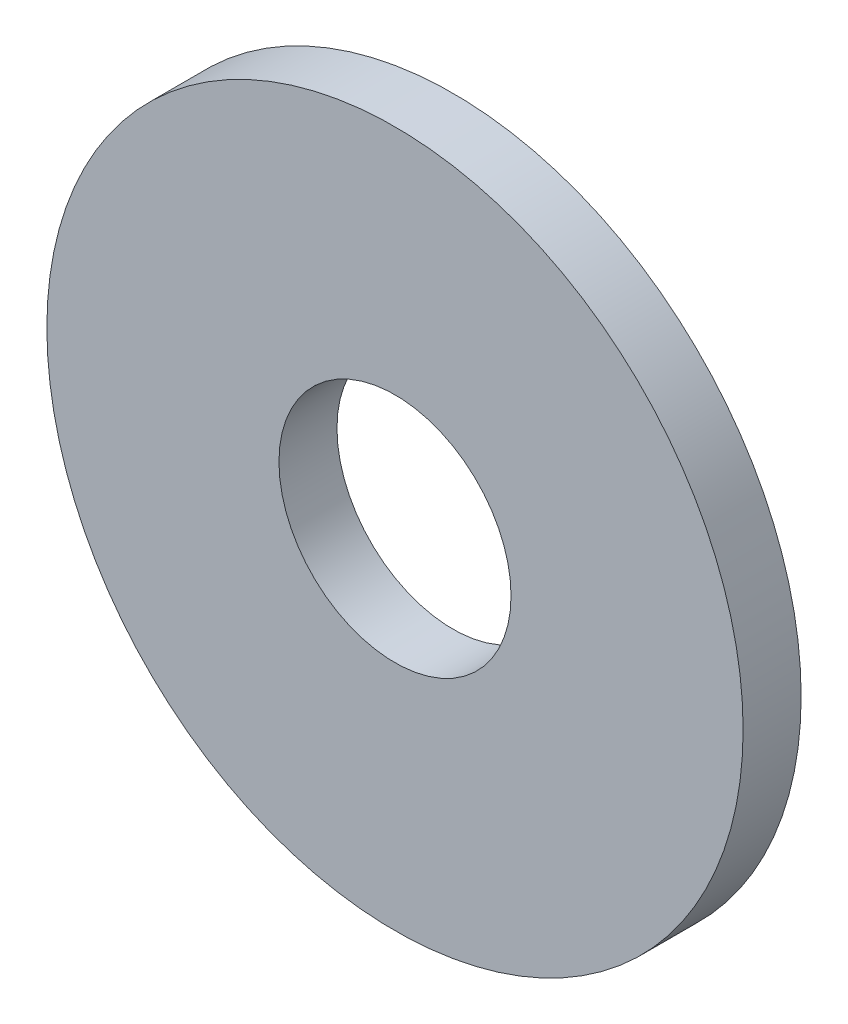
SolidWorks part; units mm, degrees
ref_plane "Front Plane" through (0, 0, 0) normal (0, 0, 1) x (1, 0, 0)
ref_plane "Top Plane" through (0, 0, 0) normal (0, 1, 0) x (1, 0, 0)
ref_plane "Right Plane" through (0, 0, 0) normal (1, 0, 0) x (0, 0, -1)
sketch "Sketch1" plane through (0, 0, 0) normal (0, 0, 1) x (1, 0, 0)
  circle A0 centre (0, 0) radius 2
  circle A1 centre (0, 0) radius 6
  dimension "D1" = 4
  dimension "D2" = 12
extrude "Boss-Extrude2" add sketch "Sketch1" along normal blind 1
